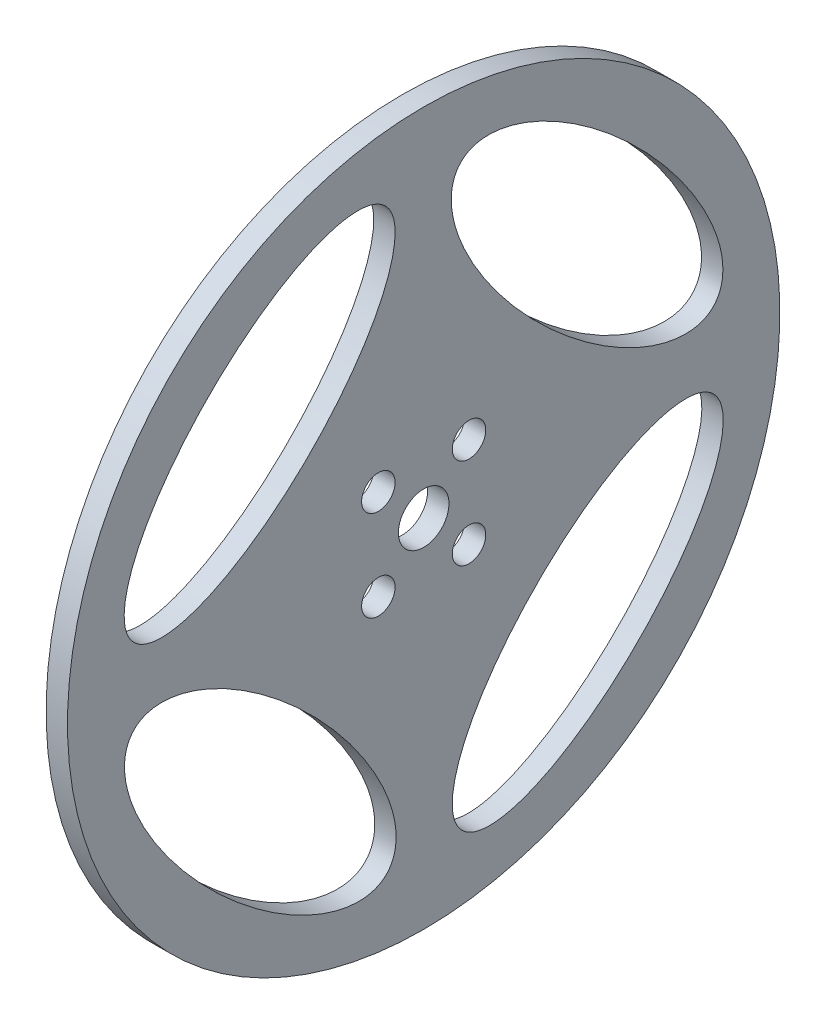
SolidWorks part; units mm, degrees
material "Acrylic (Medium-high impact)"
ref_plane "Ebene vorne" through (0, 0, 0) normal (0, 0, 1) x (1, 0, 0)
ref_plane "Ebene oben" through (0, 0, 0) normal (0, 1, 0) x (1, 0, 0)
ref_plane "Ebene rechts" through (0, 0, 0) normal (1, 0, 0) x (0, 0, -1)
sketch "Skizze1" plane through (0, 0, 0) normal (0, 0, 1) x (1, 0, 0)
  line L0 (-38.0534, 59.75) -> (-41.0534, 59.75)
  line L2 (-41.0534, 13.3) -> (-38.0534, 13.3)
  line L5 (-41.0534, 13.3) -> (-41.0534, 59.75)
  line L8 (-17.6629, 9.75) -> (-37.0534, 9.75) construction
  line L12 (-38.0534, 13.3) -> (-38.0534, 59.75)
  line L25 (-41.0534, 28.75) -> (-41.0534, 26.8663) construction
  dimension "D5" = 100
  dimension "D2" = 7.1
  dimension "D6" = 3
revolve "Rotation1" add sketch "Skizze1" angle 360 about L8
hole_wizard "Ø4.7 (4.7) Durchmesser Bohrung1" positions "Skizze3" profile "Skizze4" hole size "Ø4.7" standard "DIN" end condition through all
sketch "Skizze3" plane through (-41.0534, 11.9687, 19.8689) normal (-1, 0, 0) x (0, 0, 1)
  point P0 (-13.505, -8.5827)
  point P3 (-26.2329, -8.5827)
  point P6 (-26.2329, 4.1452)
  point P9 (-13.505, 4.1452)
sketch "Skizze4" plane through (-41.0534, 3.386, 6.364) normal (0, 1, 0) x (0, 0, 1)
  line L0 (0, 0) -> (0, 3)
  line L1 (0, 3) -> (2.35, 3)
  line L2 (2.35, 3) -> (2.35, 0)
  line L5 (2.35, 0) -> (0, 0)
  line L11 (0, -6.35) -> (0, 107.95) construction
  dimension "Bohrerdurchmesser" = 4.7
  dimension "Bohrungstiefe" = 3
sketch "Skizze5" plane through (-38.0534, 0, 0) normal (1, 0, 0) x (0, 0, -1)
  line L0 (-15.9451, 25.6246) -> (-23.0273, 32.6845) construction
  line L1 (6.364, 3.386) -> (-6.2453, 15.9555) construction
  circle A0 centre (0, 9.75) radius 22.5 construction
  ellipse E0 centre (-23.0273, 32.6845) end of major axis (-5.3776, 50.3901) minor radius 10
  dimension "D1" = 45
  dimension "D3" = 50
  dimension "D4" = 20
extrude "Schnitt-Linear austragen1" cut sketch "Skizze5" against normal up to next (3 mm away)
pattern_circular "Kreismuster1" count 4 over 360 of "Schnitt-Linear austragen1"
ref_plane "Plane1" through (-41.0534, 0, 0) normal (-1, 0, 0) x (0, 0, 1)
